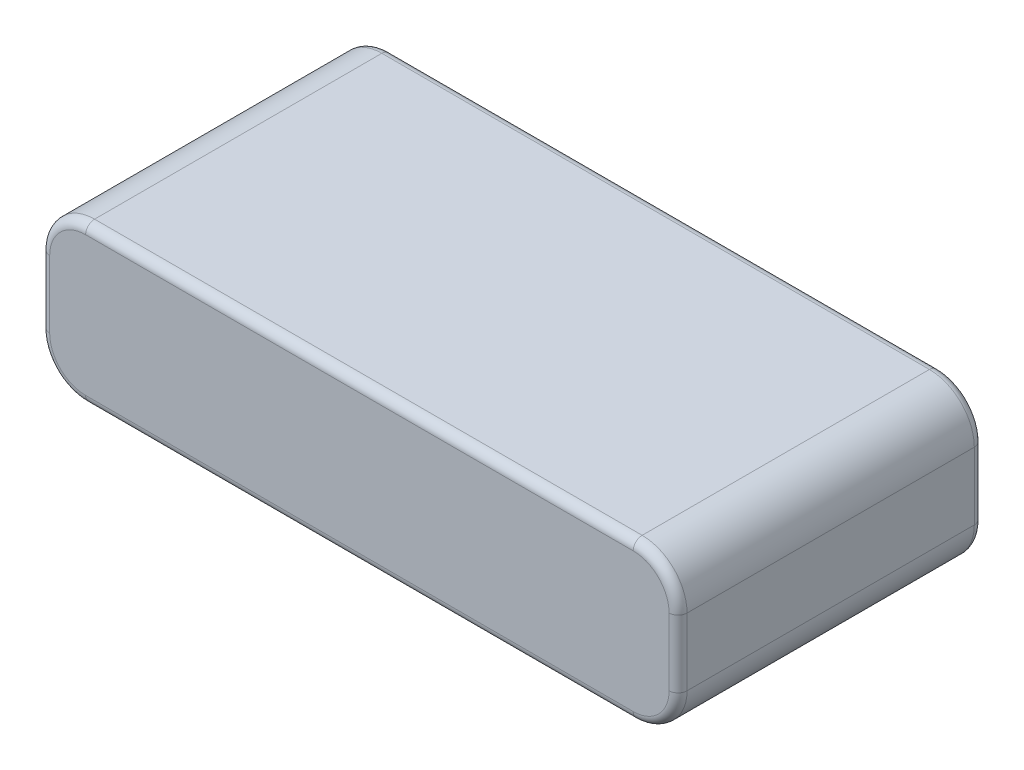
SolidWorks part; units mm, degrees
ref_plane "Front Plane" through (0, 0, 0) normal (0, 0, 1) x (1, 0, 0)
ref_plane "Top Plane" through (0, 0, 0) normal (0, 1, 0) x (1, 0, 0)
ref_plane "Right Plane" through (0, 0, 0) normal (1, 0, 0) x (0, 0, -1)
sketch "Sketch1" plane through (0, 0, 0) normal (0, 1, 0) x (1, 0, 0)
  line L1 (-35.5, -17) -> (35.5, -17)
  line L2 (-35.5, -17) -> (-35.5, 17)
  line L3 (-35.5, 17) -> (35.5, 17)
  line L4 (35.5, -17) -> (35.5, 17)
  line L5 (-35.5, -17) -> (35.5, 17) construction
  line L6 (-35.5, 17) -> (35.5, -17) construction
  point P0 (0, 0)
  dimension "D1" = 71
  dimension "D2" = 34
extrude "Boss-Extrude1" add sketch "Sketch1" along normal blind 17.5
fillet "Fillet1" radius 5 4 edges at (-35.5, 0, 0) (35.5, 0, 0) (35.5, 17.5, 0) (-35.5, 17.5, 0)
fillet "Fillet2" radius 1 16 edges at (34.0355, 1.4645, -17) (35.5, 8.75, -17) (34.0355, 16.0355, -17) (0, 17.5, -17) (-34.0355, 16.0355, -17) (-35.5, 8.75, -17) (-34.0355, 1.4645, -17) (0, 0, -17) (-34.0355, 16.0355, 17) (0, 17.5, 17) (34.0355, 16.0355, 17) (35.5, 8.75, 17) (34.0355, 1.4645, 17) (0, 0, 17) (-34.0355, 1.4645, 17) (-35.5, 8.75, 17)
